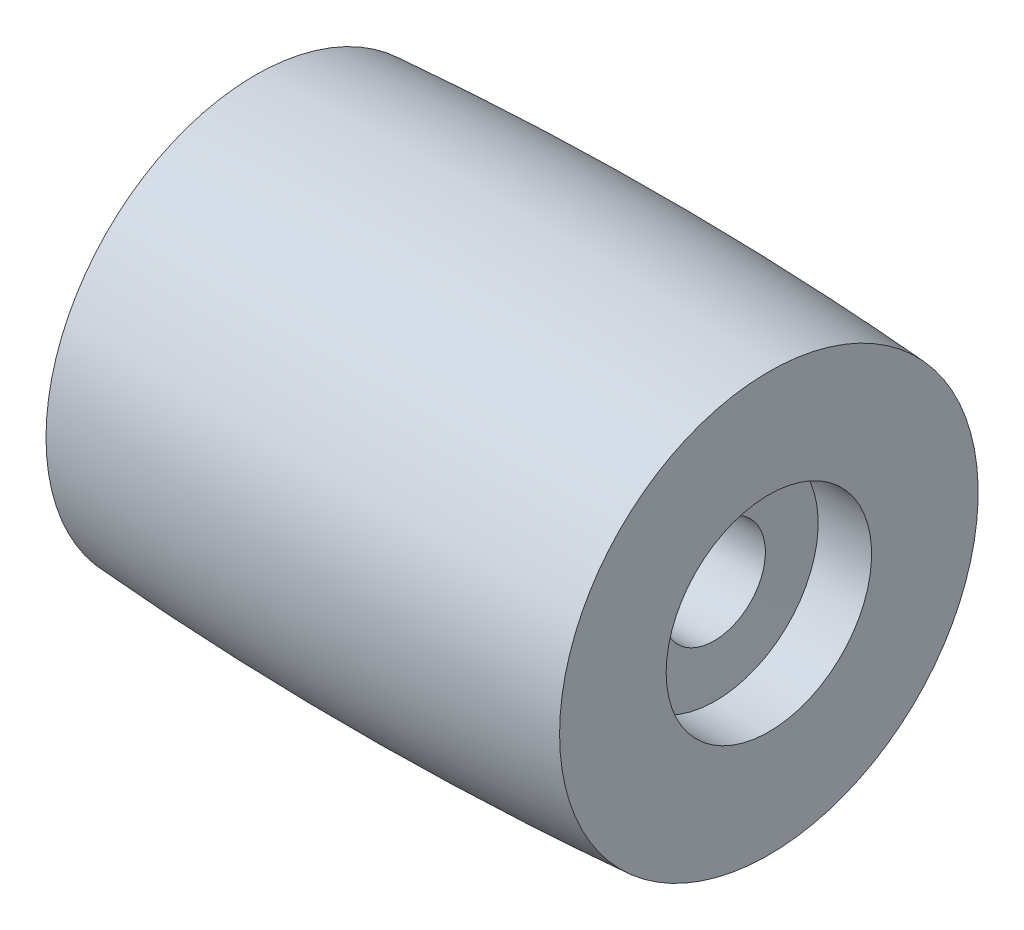
SolidWorks part; units mm, degrees
ref_plane "Front Plane" through (0, 0, 0) normal (0, 0, 1) x (1, 0, 0)
ref_plane "Top Plane" through (0, 0, 0) normal (0, 1, 0) x (1, 0, 0)
ref_plane "Right Plane" through (0, 0, 0) normal (1, 0, 0) x (0, 0, -1)
sketch "Sketch1" plane through (0, 0, 0) normal (0, 0, 1) x (1, 0, 0)
  line L0 (0, 0) -> (20.7297, 0) construction
  line L1 (0, 8.15) -> (0, 4)
  line L2 (0, 4) -> (2.0811, 4)
  line L3 (2.0811, 4) -> (2.0811, 2)
  line L4 (2.0811, 2) -> (17.8649, 2)
  line L5 (17.8649, 2) -> (17.9189, 4)
  line L6 (17.9189, 4) -> (20, 4)
  line L7 (20, 4) -> (20, 8.15)
  arc A0 (0, 8.15) -> (20, 8.15) centre (10, -141.5163) cw
  dimension "D4" = 150
  dimension "D1" = 20
  dimension "D2" = 4
  dimension "D3" = 4.15
  dimension "D5" = 2
revolve "Revolve1" add sketch "Sketch1" angle 360 about L0
